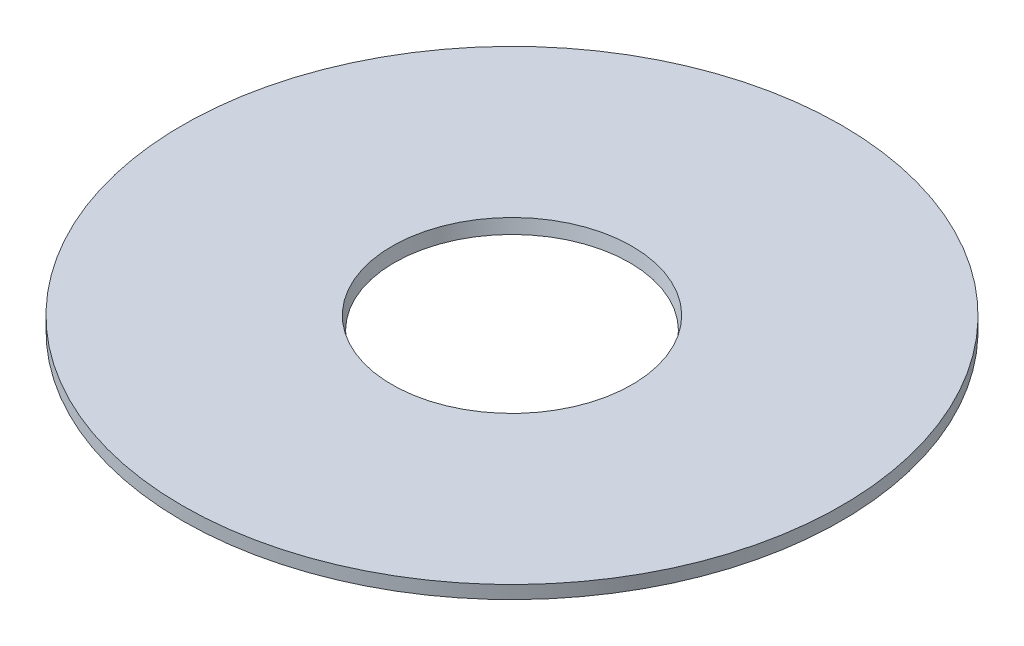
SolidWorks part; units mm, degrees
ref_plane "Front Plane" through (0, 0, 0) normal (0, 0, 1) x (1, 0, 0)
ref_plane "Top Plane" through (0, 0, 0) normal (0, 1, 0) x (1, 0, 0)
ref_plane "Right Plane" through (0, 0, 0) normal (1, 0, 0) x (0, 0, -1)
sketch "Sketch1" plane through (0, 0, 0) normal (0, 0, 1) x (1, 0, 0)
  line L0 (45.8816, 0) -> (45.8816, -5) construction
  line L1 (45.8816, -5) -> (126, -5)
  line L2 (126, -5) -> (126, 0)
  line L3 (126, 0) -> (45.8816, 0)
  line L4 (0, 0) -> (0, 74.3096) construction
  line L5 (45.8816, 0) -> (0, 0) construction
  line L8 (45.8816, 0) -> (45, -5)
  line L9 (45, -5) -> (45.8816, -5)
  dimension "D1" = 252
  dimension "D2" = 90
  dimension "D3" = 5
  dimension "D4" = 10
revolve "Revolve1" add sketch "Sketch1" angle 360 about L4
